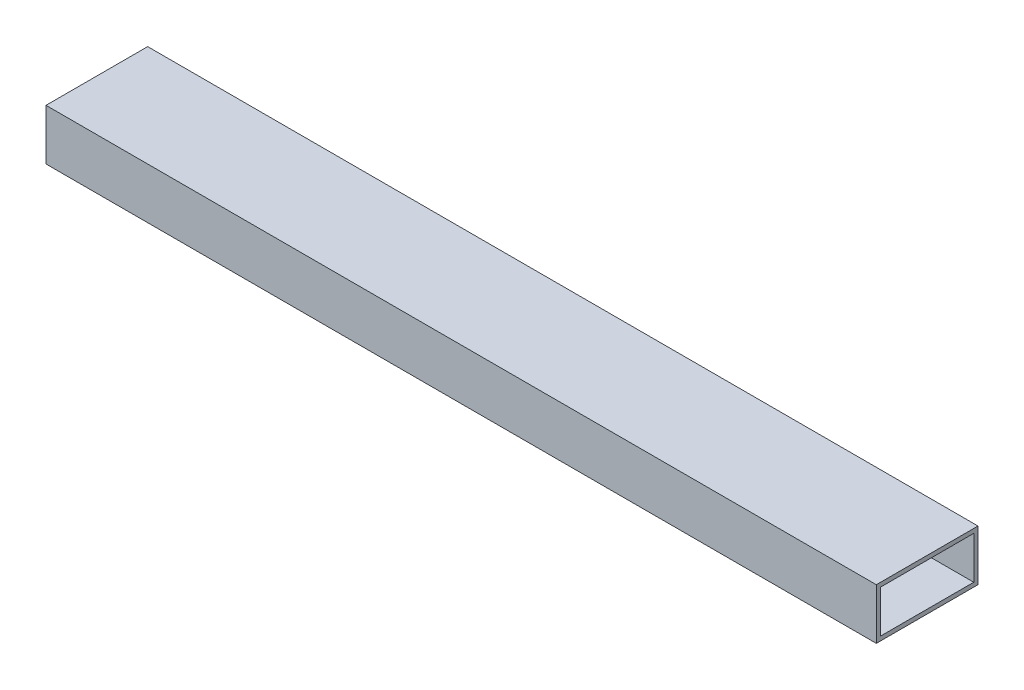
SolidWorks part; units mm, degrees
material "6061 Alloy"
ref_plane "Front Plane" through (0, 0, 0) normal (0, 0, 1) x (1, 0, 0)
ref_plane "Top Plane" through (0, 0, 0) normal (0, 1, 0) x (1, 0, 0)
ref_plane "Right Plane" through (0, 0, 0) normal (1, 0, 0) x (0, 0, -1)
sketch "Sketch1" plane through (0, 0, 0) normal (1, 0, 0) x (0, 0, -1)
  line L13 (73.025, 34.925) -> (3.175, 34.925)
  line L14 (76.2, 0) -> (0, 0)
  line L15 (76.2, 0) -> (76.2, 38.1)
  line L18 (76.2, 38.1) -> (0, 38.1)
  line L19 (0, 0) -> (0, 38.1)
  line L20 (3.175, 3.175) -> (3.175, 34.925)
  line L22 (73.025, 3.175) -> (3.175, 3.175)
  line L23 (73.025, 3.175) -> (73.025, 34.925)
  dimension "D1" = 38.1
  dimension "D3" = 3.175
  dimension "D2" = 76.2
extrude "Boss-Extrude1" add sketch "Sketch1" along normal mid plane 622.3
sketch "Sketch2" plane through (0, 0, -76.2) normal (0, 0, -1) x (-1, 0, 0)
  line L0 (-311.15, 38.1) -> (311.15, 38.1) construction
  line L1 (311.15, 0) -> (311.15, 38.1) construction
  line L2 (-311.15, 0) -> (-311.15, 38.1) construction
  point P0 (260.35, 19.05)
  point P1 (-260.35, 19.05)
  dimension "D1" = 19.05
  dimension "D2" = 50.8
  dimension "D3" = 50.8
hole_wizard "1/4-20 Tapped Hole1" positions "Sketch3" profile "Sketch4" tap size "1/4-20" standard "ANSI Inch" end condition up to next
sketch "Sketch3" plane through (0, 0, -76.2) normal (0, 0, -1) x (-1, 0, 0)
  point P0 (260.35, 19.05)
  point P3 (-260.35, 19.05)
sketch "Sketch4" plane through (-260.35, 19.05, -76.2) normal (1, 0, 0) x (0, 1, 0)
  line L0 (0, 0) -> (0, 3.175)
  line L1 (0, 3.175) -> (2.5527, 3.175)
  line L2 (2.5527, 3.175) -> (2.5527, 0)
  line L5 (2.5527, 0) -> (0, 0)
  line L11 (0, -6.35) -> (0, 107.95) construction
  dimension "Thru Tap Drill Dia." = 5.1054
  dimension "Thru Tap Drill Depth" = 3.175
cosmetic thread "Hole Thread1" parameters "D2"=6.35
cosmetic thread "Hole Thread2" parameters "D2"=6.35
